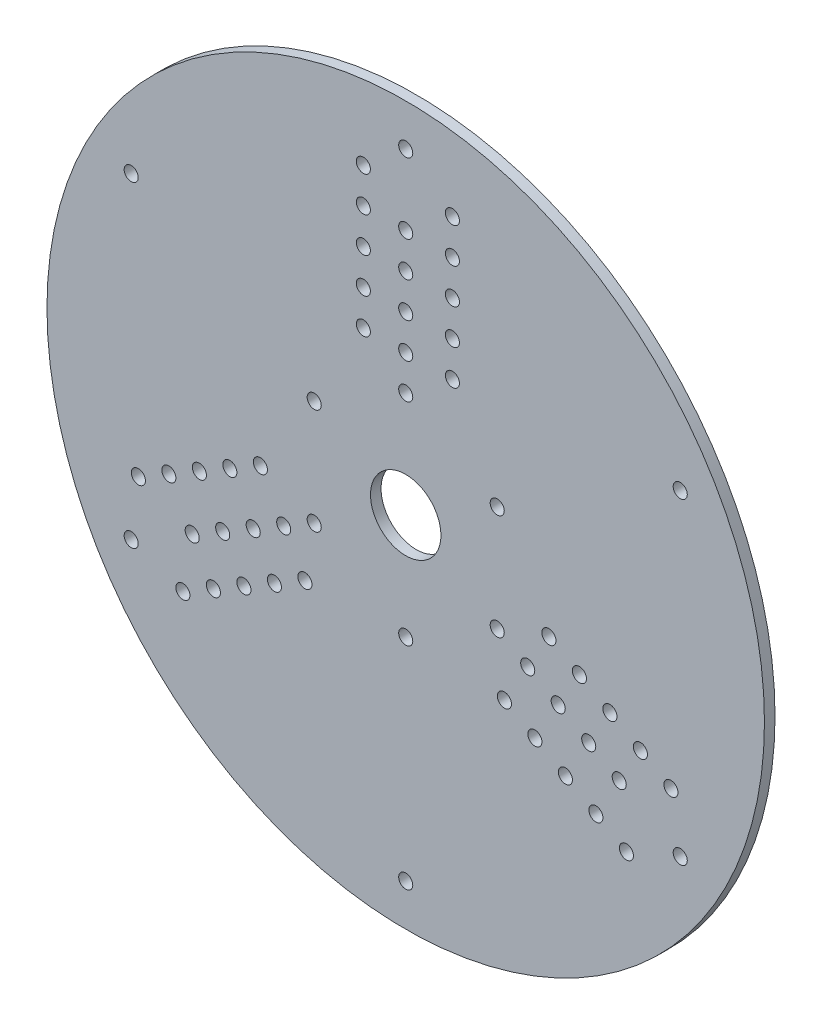
SolidWorks part; units mm, degrees
ref_plane "Front Plane" through (0, 0, 0) normal (0, 0, 1) x (1, 0, 0)
ref_plane "Top Plane" through (0, 0, 0) normal (0, 1, 0) x (1, 0, 0)
ref_plane "Right Plane" through (0, 0, 0) normal (1, 0, 0) x (0, 0, -1)
sketch "Sketch1" plane through (0, 0, 0) normal (0, 0, 1) x (1, 0, 0)
  circle A0 centre (0, 0) radius 101.8592
  circle A1 centre (0, 30) radius 2
  circle A2 centre (-12.0319, 50) radius 2
  circle A3 centre (0, 40) radius 2
  circle A4 centre (13.2521, 50) radius 2
  circle A5 centre (-12.0319, 60) radius 2
  circle A6 centre (-12.0319, 40) radius 2
  circle A7 centre (13.2521, 40) radius 2
  circle A8 centre (0, 50) radius 2
  circle A9 centre (13.2521, 60) radius 2
  circle A10 centre (-12.0319, 70) radius 2
  circle A11 centre (0, 60) radius 2
  circle A12 centre (13.2521, 70) radius 2
  circle A13 centre (-12.0319, 80) radius 2
  circle A14 centre (0, 70) radius 2
  circle A15 centre (13.2521, 80) radius 2
  circle A16 centre (25.9808, -15) radius 2
  circle A17 centre (49.3172, -14.5801) radius 2
  circle A18 centre (34.641, -20) radius 2
  circle A19 centre (36.6752, -36.4766) radius 2
  circle A20 centre (57.9775, -19.5801) radius 2
  circle A21 centre (40.657, -9.5801) radius 2
  circle A22 centre (28.015, -31.4766) radius 2
  circle A23 centre (43.3013, -25) radius 2
  circle A24 centre (45.3355, -41.4766) radius 2
  circle A25 centre (66.6377, -24.5801) radius 2
  circle A26 centre (51.9615, -30) radius 2
  circle A27 centre (53.9957, -46.4766) radius 2
  circle A28 centre (75.298, -29.5801) radius 2
  circle A29 centre (60.6218, -35) radius 2
  circle A30 centre (62.656, -51.4766) radius 2
  circle A31 centre (-25.9808, -15) radius 2
  circle A32 centre (-37.2853, -35.4199) radius 2
  circle A33 centre (-34.641, -20) radius 2
  circle A34 centre (-49.9273, -13.5234) radius 2
  circle A35 centre (-45.9456, -40.4199) radius 2
  circle A36 centre (-28.6251, -30.4199) radius 2
  circle A37 centre (-41.267, -8.5234) radius 2
  circle A38 centre (-43.3013, -25) radius 2
  circle A39 centre (-58.5876, -18.5234) radius 2
  circle A40 centre (-54.6058, -45.4199) radius 2
  circle A41 centre (-51.9615, -30) radius 2
  circle A42 centre (-67.2478, -23.5234) radius 2
  circle A43 centre (-63.2661, -50.4199) radius 2
  circle A44 centre (-60.6218, -35) radius 2
  circle A45 centre (-75.9081, -28.5234) radius 2
  circle A46 centre (77.9423, 45) radius 2
  circle A47 centre (77.9423, -45) radius 2
  circle A48 centre (0, -90) radius 2
  circle A49 centre (-77.9423, -45) radius 2
  circle A50 centre (-77.9423, 45) radius 2
  circle A51 centre (0, 90) radius 2
  circle A52 centre (0, 0) radius 10
  circle A53 centre (25.9808, 15) radius 2
  circle A54 centre (0, -30) radius 2
  circle A55 centre (-25.9808, 15) radius 2
  point P96 (0, 0)
  point P109 (0, 0)
  point P117 (0, 0)
  dimension "D1" = 203.7183
  dimension "D3" = 4
  dimension "D5" = 4
  dimension "D6" = 4
  dimension "D8" = 4
  dimension "D12" = 20
  dimension "D13" = 4
  dimension "D2" = 30
  dimension "D4" = 5
  dimension "D9" = 90
  dimension "D10" = 60
  dimension "D14" = 60
  dimension "D15" = 30
  dimension "D7" = 3
  dimension "D11" = 6
  dimension "D16" = 3
extrude "Boss-Extrude1" add sketch "Sketch1" along normal blind 3
